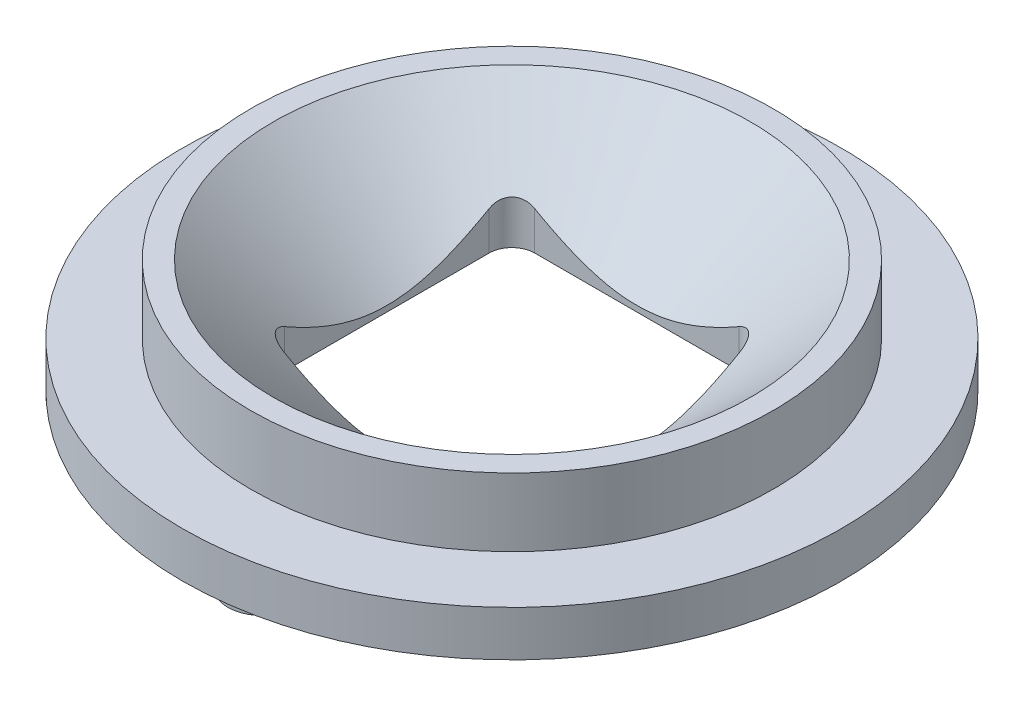
SolidWorks part; units mm, degrees
ref_plane "Front Plane" through (0, 0, 0) normal (0, 0, 1) x (1, 0, 0)
ref_plane "Top Plane" through (0, 0, 0) normal (0, 1, 0) x (1, 0, 0)
ref_plane "Right Plane" through (0, 0, 0) normal (1, 0, 0) x (0, 0, -1)
sketch "Sketch1" plane through (0, 0, 0) normal (0, 1, 0) x (1, 0, 0)
  circle A0 centre (0, 0) radius 14.5
  dimension "D1" = 29
extrude "Body" add sketch "Sketch1" along normal blind 2
sketch "Sketch2" plane through (0, 0, 0) normal (0, -1, 0) x (1, 0, 0)
  line L0 (55, 0) -> (-55, 0) construction
  line L1 (-17.9272, 0) -> (0, 0) construction
  line L2 (0, 17.4569) -> (0, -2.6282) construction
  circle A4 centre (0, 11) radius 1.5
  circle A5 centre (0, -11) radius 1.5
  point P13 (0, 0)
  dimension "D1" = 3
  dimension "D2" = 11
  dimension "D3" = 2
extrude "FixHoles" add sketch "Sketch2" along normal blind 2
sketch "Sketch3" plane through (0, 2, 0) normal (0, 1, 0) x (1, 0, 0)
  circle A0 centre (0, 0) radius 11.5
  dimension "D1" = 23
extrude "Body2" add sketch "Sketch3" along normal blind 3
sketch "Sketch5" plane through (0, 0, 0) normal (0, -1, 0) x (1, 0, 0)
  line L1 (5.5, 5.5) -> (-5.5, 5.5)
  line L2 (5.5, 5.5) -> (5.5, -5.5)
  line L3 (5.5, -5.5) -> (-5.5, -5.5)
  line L4 (-5.5, 5.5) -> (-5.5, -5.5)
  line L5 (5.5, 5.5) -> (-5.5, -5.5) construction
  line L6 (5.5, -5.5) -> (-5.5, 5.5) construction
  point P0 (0, 0)
  dimension "D1" = 11
  dimension "D2" = 11
extrude "Window_hole" cut sketch "Sketch5" against normal blind 12
sketch "Sketch6" plane through (0, 0, 0) normal (0, 0, 1) x (1, 0, 0)
  line L0 (-5.5, 5) -> (-10.5, 5)
  line L1 (11.5, 5) -> (-11.5, 5) construction
  line L2 (-10.5, 5) -> (-5.5, 0.5)
  line L3 (-5.5, 5) -> (-5.5, 0) construction
  line L4 (-5.5, 0.5) -> (-5.5, 5)
  line L5 (0, 7.3753) -> (0, -2.8005) construction
  dimension "D1" = 5
  dimension "D2" = 4.5
revolve "Objective_cut" cut sketch "Sketch6" angle 360 about L5
sketch "Sketch7" plane through (0, 0, 0) normal (0, -1, 0) x (1, 0, 0)
  line L1 (6.5, -6.5) -> (-6.5, -6.5)
  line L2 (6.5, -6.5) -> (6.5, 6.5)
  line L3 (6.5, 6.5) -> (-6.5, 6.5)
  line L4 (-6.5, -6.5) -> (-6.5, 6.5)
  line L5 (6.5, -6.5) -> (-6.5, 6.5) construction
  line L6 (6.5, 6.5) -> (-6.5, -6.5) construction
  point P0 (0, 0)
  dimension "D1" = 13
  dimension "D2" = 13
extrude "Window" cut sketch "Sketch7" against normal blind 0.25
fillet "Window_Fillet" radius 1 4 edges at (-5.5, 1.4002, 5.5) (5.5, 1.4002, 5.5) (5.5, 1.4002, -5.5) (-5.5, 1.4002, -5.5)
